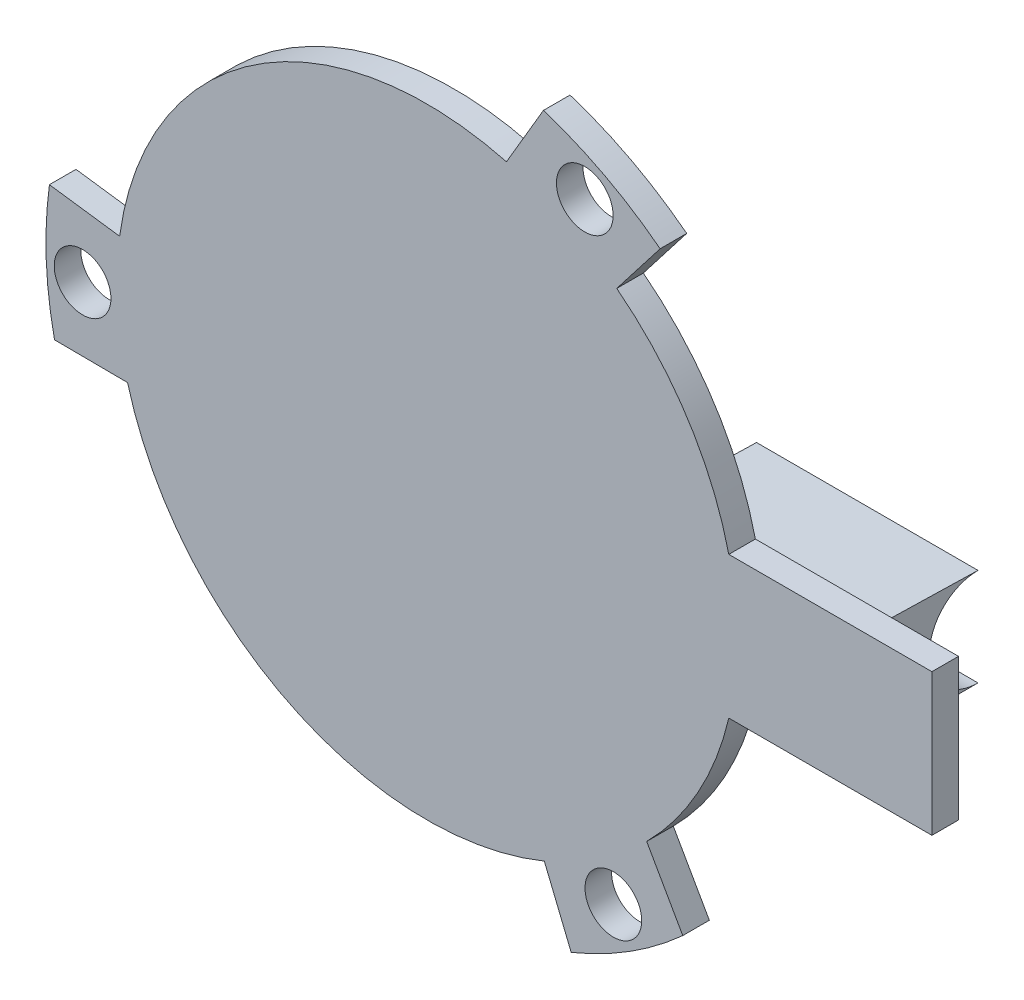
SolidWorks part; units mm, degrees
ref_plane "Front Plane" through (0, 0, 0) normal (0, 0, 1) x (1, 0, 0)
ref_plane "Top Plane" through (0, 0, 0) normal (0, 1, 0) x (1, 0, 0)
ref_plane "Right Plane" through (0, 0, 0) normal (1, 0, 0) x (0, 0, -1)
sketch "Sketch1" plane through (0, 0, 0) normal (0, 0, 1) x (1, 0, 0)
  line L0 (6.6268, -16.1968) -> (8.1415, -19.8989) construction
  line L1 (14.4391, -15.9299) -> (12.4034, -12.3453) construction
  line L2 (10.7134, 13.8373) -> (13.1622, 17.0002) construction
  line L3 (6.5761, 20.4696) -> (4.4896, 16.9143) construction
  line L4 (-17.3402, 2.3594) -> (-21.3037, 2.8987) construction
  line L5 (-21.0153, -4.5397) -> (-16.893, -4.569) construction
  line L6 (6.6268, -16.1968) -> (8.1415, -19.8989)
  line L7 (14.4391, -15.9299) -> (12.4034, -12.3453)
  line L8 (10.7134, 13.8373) -> (13.1622, 17.0002)
  line L9 (6.5761, 20.4696) -> (4.4896, 16.9143)
  line L10 (-17.3402, 2.3594) -> (-21.3037, 2.8987)
  line L11 (-21.0153, -4.5397) -> (-16.893, -4.569)
  line L12 (17.0367, 4) -> (28.5, 4)
  line L13 (28.5, 4) -> (28.5, -4)
  line L14 (28.5, -4) -> (17.0367, -4)
  arc A0 (6.6268, -16.1968) -> (12.4034, -12.3453) centre (0, 0) ccw construction
  arc A1 (8.1415, -19.8989) -> (14.4391, -15.9299) centre (0, 0) ccw construction
  arc A2 (10.7134, 13.8373) -> (4.4896, 16.9143) centre (0, 0) ccw construction
  arc A3 (13.1622, 17.0002) -> (6.5761, 20.4696) centre (0, 0) ccw construction
  arc A4 (-17.3402, 2.3594) -> (-16.893, -4.569) centre (0, 0) ccw construction
  arc A5 (-21.3037, 2.8987) -> (-21.0153, -4.5397) centre (0, 0) ccw construction
  arc A6 (6.6268, -16.1968) -> (12.4034, -12.3453) centre (0, 0) ccw
  arc A7 (8.1415, -19.8989) -> (14.4391, -15.9299) centre (0, 0) ccw
  arc A8 (10.7134, 13.8373) -> (4.4896, 16.9143) centre (0, 0) ccw
  arc A9 (13.1622, 17.0002) -> (6.5761, 20.4696) centre (0, 0) ccw
  arc A10 (-17.3402, 2.3594) -> (-16.893, -4.569) centre (0, 0) ccw
  arc A11 (-21.3037, 2.8987) -> (-21.0153, -4.5397) centre (0, 0) ccw
  arc A12 (17.0367, 4) -> (17.0367, -4) centre (0, 0) ccw
  circle A13 centre (-19.4318, -0.9308) radius 1.6
  circle A14 centre (8.9098, 17.2938) radius 1.6
  circle A15 centre (10.522, -16.363) radius 1.6
extrude "Boss-Extrude1" add sketch "Sketch1" along normal blind 1.5 contours L10 A11 L11 A10 A13 | L12 A12 A8 A10 A6 L14 L13 | L8 A9 L9 A8 A14 | L6 A7 L7 A6 A15
sketch "Sketch2" plane through (28.5, 0, 0) normal (1, 0, 0) x (0, 0, -1)
  line L0 (6, 2.75) -> (0, 2.8987)
  line L1 (6, -2.75) -> (0, -2.753)
  line L2 (13, -2.753) -> (0, -2.753) construction
  line L4 (0, -4) -> (0, 4)
  line L5 (0, 4) -> (-1.5, 4)
  line L6 (-1.5, 4) -> (-1.5, -4)
  line L7 (-1.5, -4) -> (0, -4)
  line L8 (0, -4) -> (0, 4)
  line L9 (0, 4) -> (-1.5, 4)
  line L10 (-1.5, 4) -> (-1.5, -4)
  line L11 (-1.5, -4) -> (0, -4)
  arc A2 (6, 2.75) -> (6, -2.75) centre (6, 0) ccw
  line M6 (0, -4) -> (0, 4)
  dimension "D1" = 0
extrude "Boss-Extrude2" add sketch "Sketch2" against normal blind 12.5 from surface at -4.9 contours A2 L0 L1 M6
